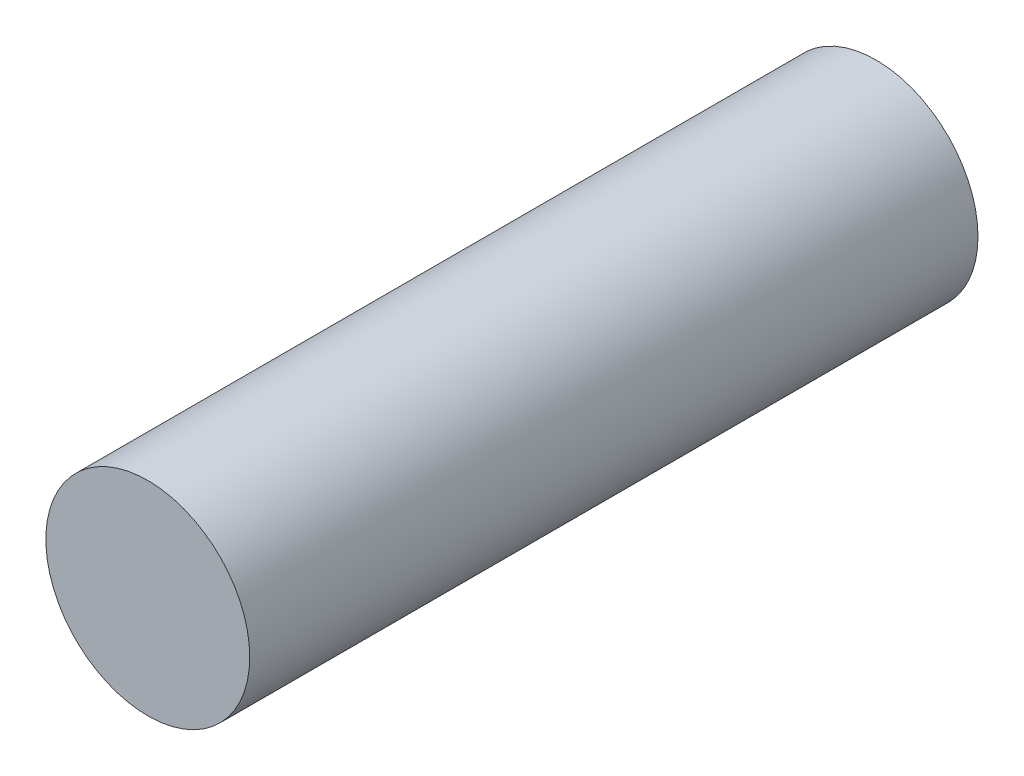
SolidWorks part; units mm, degrees
ref_plane "Front Plane" through (0, 0, 0) normal (0, 0, 1) x (1, 0, 0)
ref_plane "Top Plane" through (0, 0, 0) normal (0, 1, 0) x (1, 0, 0)
ref_plane "Right Plane" through (0, 0, 0) normal (1, 0, 0) x (0, 0, -1)
sketch "Sketch1" plane through (0, 0, 0) normal (0, 0, 1) x (1, 0, 0)
  circle A0 centre (0, 0) radius 1.4
  dimension "D1" = 2.8
extrude "Boss-Extrude1" add sketch "Sketch1" along normal blind 10
